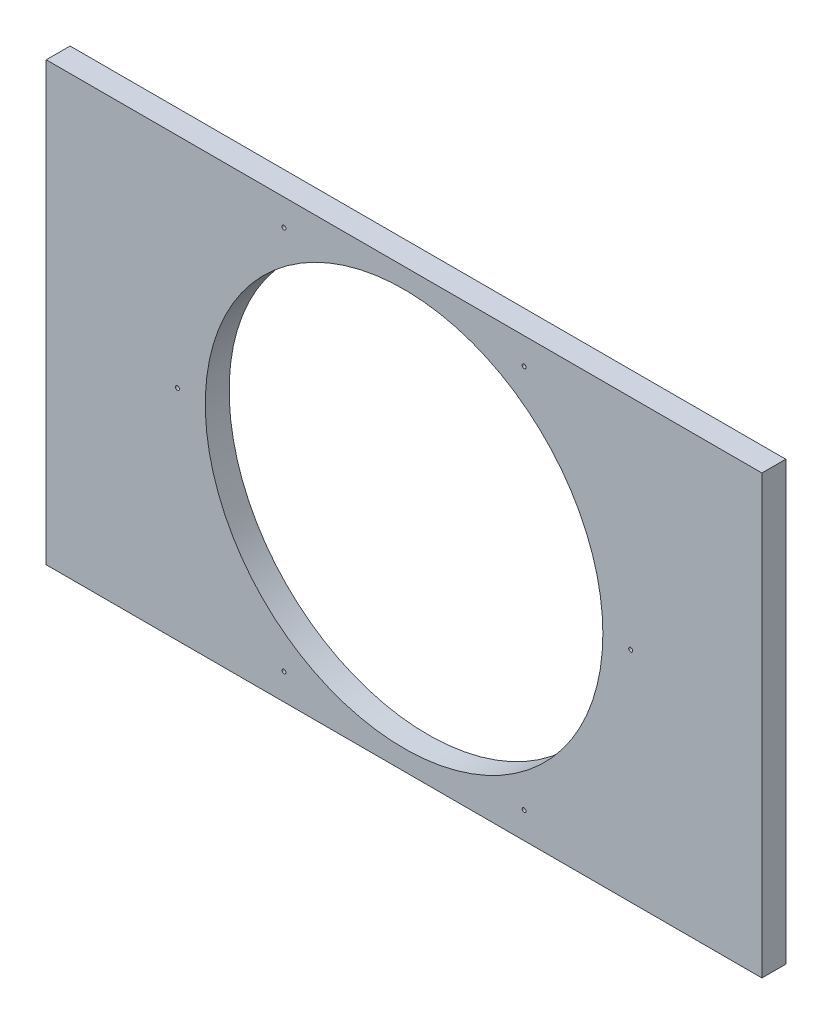
SolidWorks part; units mm, degrees
ref_plane "Front Plane" through (0, 0, 0) normal (0, 0, 1) x (1, 0, 0)
ref_plane "Top Plane" through (0, 0, 0) normal (0, 1, 0) x (1, 0, 0)
ref_plane "Right Plane" through (0, 0, 0) normal (1, 0, 0) x (0, 0, -1)
sketch "Sketch1" plane through (0, 0, 0) normal (0, 0, 1) x (1, 0, 0)
  line L1 (0, 0) -> (180, 0)
  line L2 (0, 0) -> (0, 110)
  line L3 (0, 110) -> (180, 110)
  line L4 (180, 0) -> (180, 110)
sketch "Sketch2" plane through (0, 0, 0) normal (0, 0, 1) x (1, 0, 0)
  circle A0 centre (90, 55) radius 50
extrude "Boss-Extrude1" add sketch "Sketch1" along normal blind 6 contours L3 L4 L1 L2
extrude "Cut-Extrude1" cut sketch "Sketch2" along normal blind 6
ref_plane "Plane1" through (0, 0, 6) normal (0, 0, 1) x (1, 0, 0)
sketch "Sketch3" plane through (0, 0, 6) normal (0, 0, 1) x (1, 0, 0)
  point P0 (90, 55)
sketch "Sketch4" plane through (0, 0, 0) normal (0, 0, 1) x (1, 0, 0)
  line L0 (33, 55) -> (147, 55) construction
  line L1 (59.7946, 6.6613) -> (120.2054, 103.3387) construction
  line L2 (59.7946, 103.3387) -> (120.2054, 6.6613) construction
  circle A0 centre (59.7946, 103.3387) radius 0.5
  circle A1 centre (120.2054, 103.3387) radius 0.5
  circle A2 centre (147, 55) radius 0.5
  circle A3 centre (120.2054, 6.6613) radius 0.5
  circle A4 centre (59.7946, 6.6613) radius 0.5
  circle A5 centre (33, 55) radius 0.5
  point P4 (90, 55)
  point P9 (90, 55)
  point P12 (90, 55)
extrude "Cut-Extrude2" cut sketch "Sketch4" along normal blind 40
